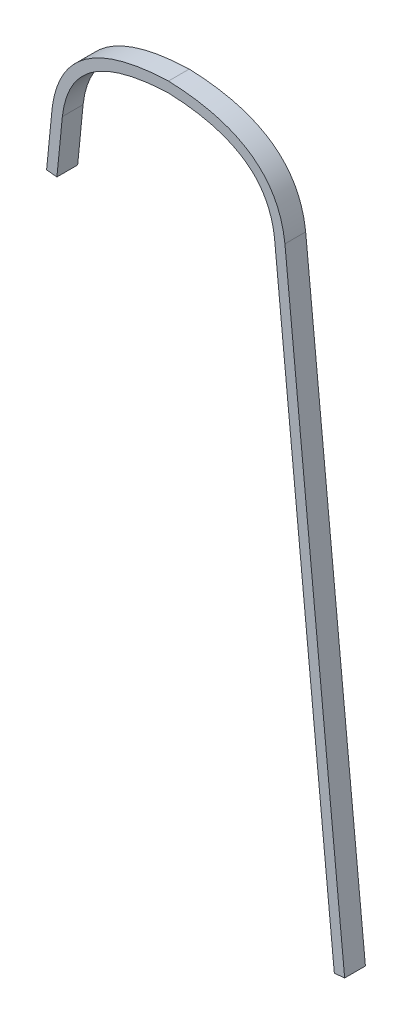
SolidWorks part; units mm, degrees
ref_plane "Front Plane" through (0, 0, 0) normal (0, 0, 1) x (1, 0, 0)
ref_plane "Top Plane" through (0, 0, 0) normal (0, 1, 0) x (1, 0, 0)
ref_plane "Right Plane" through (0, 0, 0) normal (1, 0, 0) x (0, 0, -1)
sketch "Sketch1" plane through (0, 0, 0) normal (0, 0, 1) x (1, 0, 0)
  line L0 (152.2242, 179.7953) -> (97.404, 735.8286)
  line L1 (-102.3813, 685.3442) -> (-97.404, 735.8286)
  line L2 (-111.8604, 686.2788) -> (-102.3813, 685.3442)
  line L3 (152.2242, 179.7953) -> (161.7032, 180.7299)
  line L4 (-166.6875, 130.175) -> (-106.8761, 736.8337) construction
  line L5 (-156.6942, 134.4562) -> (-97.404, 735.8286) construction
  line L6 (-111.8604, 686.2788) -> (-106.8761, 736.8337)
  line L7 (161.7032, 180.7299) -> (106.8761, 736.8337)
  line L8 (0, 0) -> (-166.6875, 130.175) construction
  line L9 (0, 12.0854) -> (-156.6942, 134.4562) construction
  line L10 (0, 0) -> (166.6875, 130.175) construction
  line L11 (0, 12.0854) -> (156.6942, 134.4562) construction
  line L12 (166.6875, 130.175) -> (106.8761, 736.8337) construction
  line L13 (156.6942, 134.4562) -> (97.404, 735.8286) construction
  spline S1 degree 2 poles (-106.8761, 736.8337) (-98.6556, 809.3851) (0, 812.8) knots 0 0 0 1 1 1
  spline S3 degree 2 poles (106.8761, 736.8337) (98.6556, 809.3851) (0, 812.8) knots 0 0 0 1 1 1
  spline S4 degree 1 poles (-97.404, 735.8286) (0, 803.2691) knots 0 0 1 1 construction
  spline S5 degree 1 poles (97.404, 735.8286) (0, 803.2691) knots 0 0 1 1 construction
  spline S8 degree 3 poles (-97.404, 735.8286) (-97.3262, 736.511) (-97.1554, 737.882) (-96.764, 740.5535) (-96.1774, 743.8053) (-95.3214, 747.555) (-93.9799, 752.3593) (-91.9331, 758.0032) (-88.8953, 764.2283) (-85.2743, 769.9432) (-79.6482, 776.9324) (-71.0508, 784.5724) (-60.1295, 790.8325) (-49.8978, 794.9673) (-41.467, 797.6141) (-32.2731, 799.7901) (-23.9758, 801.1984) (-16.9573, 802.076) (-11.5049, 802.6082) (-6.8004, 802.946) (-2.9501, 803.1519) (-0.9798, 803.2339) (0, 803.2691) knots 0.000508 0.000508 0.000508 0.000508 0.016098 0.031688 0.062868 0.094048 0.125228 0.187588 0.249948 0.312308 0.374668 0.499388 0.624108 0.686468 0.748828 0.811188 0.873548 0.904727 0.935907 0.967087 0.982677 0.998267 0.998267 0.998267 0.998267
  spline S9 degree 3 poles (0, 803.2691) (0.9798, 803.2339) (2.9501, 803.1519) (6.8004, 802.946) (11.5049, 802.6082) (16.9573, 802.076) (23.9758, 801.1984) (32.2731, 799.7901) (41.467, 797.6141) (49.8978, 794.9673) (60.1295, 790.8325) (71.0508, 784.5724) (79.6482, 776.9324) (85.2743, 769.9432) (88.8953, 764.2283) (91.9331, 758.0032) (93.9799, 752.3593) (95.3214, 747.555) (96.1774, 743.8053) (96.764, 740.5535) (97.1554, 737.882) (97.3262, 736.511) (97.404, 735.8286) knots 0.000508 0.000508 0.000508 0.000508 0.016098 0.031688 0.062868 0.094048 0.125228 0.187588 0.249948 0.312308 0.374668 0.499388 0.624108 0.686468 0.748828 0.811188 0.873548 0.904727 0.935907 0.967087 0.982677 0.998267 0.998267 0.998267 0.998267
  dimension "D3" = 9.525
  dimension "D4" = 50.8
extrude "Boss-Extrude1" add sketch "Sketch1" along normal blind 19.05
